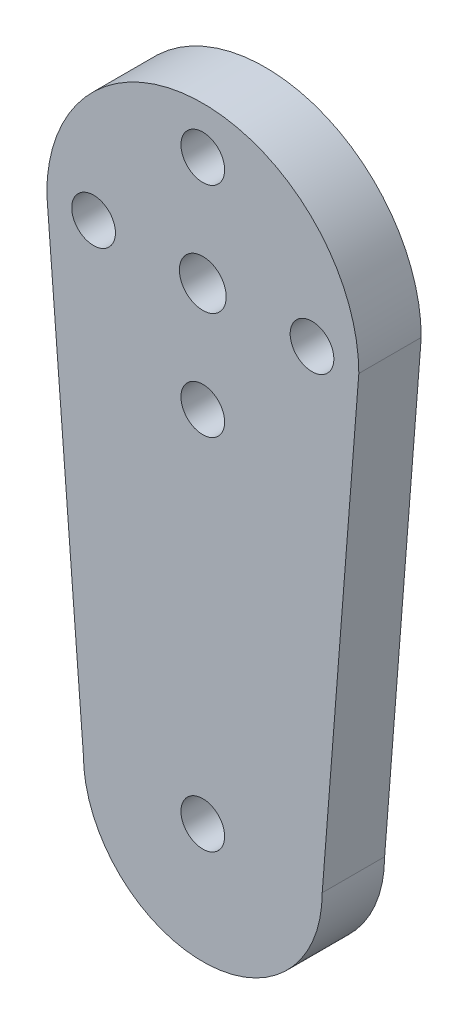
SolidWorks part; units mm, degrees
ref_plane "Front Plane" through (0, 0, 0) normal (0, 0, 1) x (1, 0, 0)
ref_plane "Top Plane" through (0, 0, 0) normal (0, 1, 0) x (1, 0, 0)
ref_plane "Right Plane" through (0, 0, 0) normal (1, 0, 0) x (0, 0, -1)
sketch "Sketch1" plane through (0, 0, 0) normal (0, 0, 1) x (1, 0, 0)
  line L0 (-10, 0) -> (-7.6529, -30)
  line L1 (10, 0) -> (7.6529, -30)
  line L2 (0, 5.6) -> (0, 1.5)
  arc A0 (10, 0) -> (-10, 0) centre (0, 0) ccw
  circle A2 centre (0, 0) radius 1.5
  circle A4 centre (7, 0) radius 1.4
  circle A5 centre (0, -7) radius 1.4
  circle A6 centre (-7, 0) radius 1.4
  circle A7 centre (0, 7) radius 1.4
  circle A8 centre (0, -30) radius 1.4
  arc A9 (-7.6529, -30) -> (7.6529, -30) centre (0, -30) ccw
  point P18 (0, 0)
  dimension "D1" = 20
  dimension "D3" = 3
  dimension "D6" = 2.8
  dimension "D10" = 2.8
  dimension "D7" = 7
  dimension "D9" = 4.1
  dimension "D11" = 30
  dimension "D8" = 4
extrude "Boss-Extrude1" add sketch "Sketch1" along normal blind 4 contours A6 | A7 | A2 | A4 | A5 | A8 | A9 L1 A0 L0
